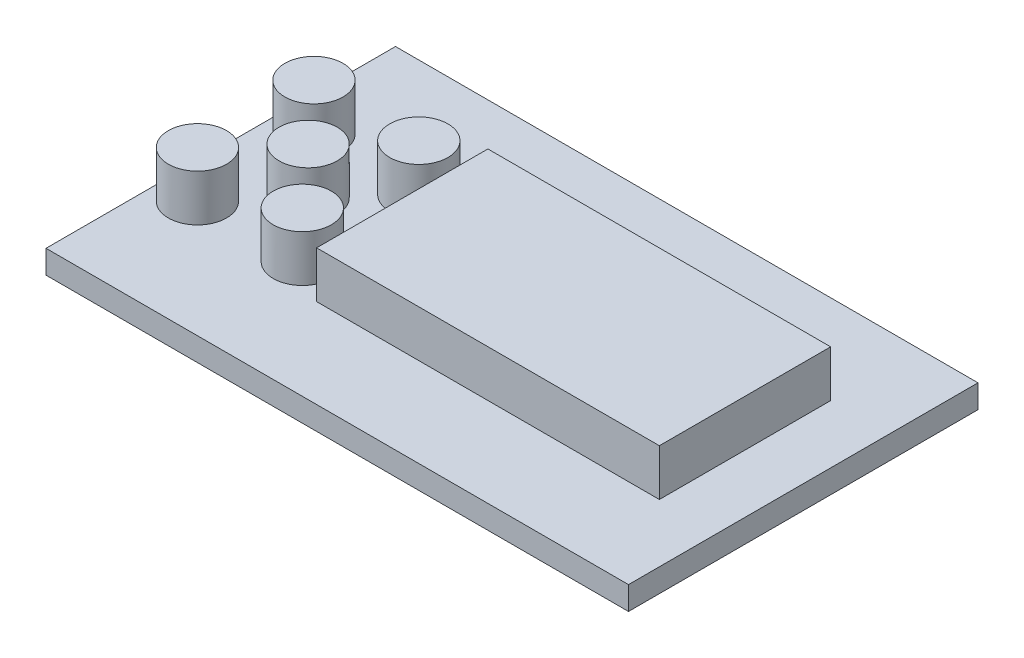
SolidWorks part; units mm, degrees
ref_plane "前视基准面" through (0, 0, 0) normal (0, 0, 1) x (1, 0, 0)
ref_plane "上视基准面" through (0, 0, 0) normal (0, 1, 0) x (1, 0, 0)
ref_plane "右视基准面" through (0, 0, 0) normal (1, 0, 0) x (0, 0, -1)
sketch "草图1" plane through (0, 0, 0) normal (0, 1, 0) x (1, 0, 0)
  line L1 (25, 15) -> (-25, 15)
  line L2 (25, 15) -> (25, -15)
  line L3 (25, -15) -> (-25, -15)
  line L4 (-25, 15) -> (-25, -15)
  line L5 (0, -15) -> (0, 15) construction
  line L6 (25, 0) -> (-25, 0) construction
  point P0 (0, 0)
  dimension "D1" = 50
  dimension "D2" = 30
extrude "凸台-拉伸1" add sketch "草图1" along normal blind 2
sketch "草图2" plane through (0, 2, 0) normal (0, 1, 0) x (1, 0, 0)
  line L0 (0, 0) -> (66.3856, 0) construction
  line L1 (20, 7.35) -> (-9.42, 7.35)
  line L2 (20, 7.35) -> (20, -7.35)
  line L3 (20, -7.35) -> (-9.42, -7.35)
  line L4 (-9.42, 7.35) -> (-9.42, -7.35)
  line L5 (25, -15) -> (25, 15) construction
  dimension "D1" = 14.7
  dimension "D2" = 29.42
  dimension "D3" = 5
extrude "凸台-拉伸2" add sketch "草图2" along normal blind 4
sketch "草图3" plane through (0, 0, 0) normal (0, -1, 0) x (-1, 0, 0)
  line L0 (0, 0) -> (-22.6279, 0) construction
  line L1 (-25, -15) -> (-25, 15) construction
  line L2 (-24, -7.5) -> (0, -7.5)
  line L3 (-24, -7.5) -> (-24, 7.5)
  line L4 (-24, 7.5) -> (0, 7.5)
  line L5 (0, -7.5) -> (0, 7.5)
  line L6 (-12, 7.5) -> (-12, -7.5) construction
  line L7 (-24, 0) -> (0, 0) construction
  point P2 (-12, 0)
  dimension "D1" = 24
  dimension "D2" = 15
  dimension "D3" = 1
extrude "凸台-拉伸3" add sketch "草图3" along normal blind 1
sketch "草图4" plane through (0, -1, 0) normal (0, -1, 0) x (1, 0, 0)
  line L1 (17, 6.5) -> (1, 6.5)
  line L2 (17, 6.5) -> (17, -6.5)
  line L3 (17, -6.5) -> (1, -6.5)
  line L4 (1, 6.5) -> (1, -6.5)
  line L5 (9, -6.5) -> (9, 6.5) construction
  line L6 (17, 0) -> (1, 0) construction
  line L7 (0, 7.5) -> (0, -7.5) construction
  line L8 (24, 7.5) -> (0, 7.5) construction
  line L9 (0, -7.5) -> (24, -7.5) construction
  point P0 (9, 0)
  dimension "D1" = 1
  dimension "D2" = 1
  dimension "D3" = 1
  dimension "D4" = 16
extrude "凸台-拉伸4" add sketch "草图4" along normal blind 2
sketch "草图5" plane through (0, 2, 0) normal (0, 1, 0) x (1, 0, 0)
  line L0 (0, 0) -> (-38.0168, 0) construction
  line L1 (-25, 15) -> (-25, -15) construction
  line L2 (-22, 5) -> (-13, 5) construction
  line L3 (-22, 5) -> (-22, -5) construction
  line L4 (-22, -5) -> (-13, -5) construction
  line L5 (-13, 5) -> (-13, -5) construction
  line L6 (-17.5, -5) -> (-17.5, 5) construction
  line L7 (-22, 0) -> (-13, 0) construction
  line L8 (-9.42, 7.35) -> (-9.42, -7.35) construction
  circle A0 centre (-22, 5) radius 2.5
  circle A1 centre (-22, -5) radius 2.5
  circle A2 centre (-13, -5) radius 2.5
  circle A3 centre (-13, 5) radius 2.5
  circle A4 centre (-17.5, 0) radius 2.5
  point P1 (-17.5, 0)
  dimension "D1" = 5
  dimension "D2" = 3
  dimension "D3" = 5
  dimension "D4" = 9
  dimension "D5" = 3.58
extrude "凸台-拉伸5" add sketch "草图5" along normal blind 4
